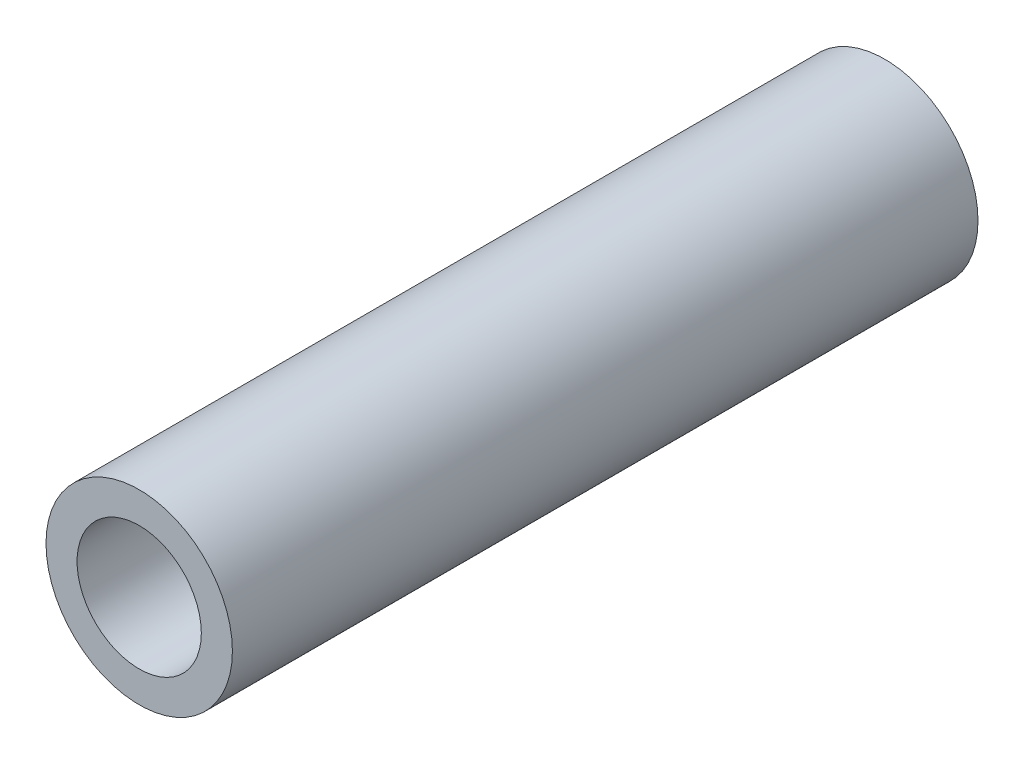
SolidWorks part; units mm, degrees
ref_plane "Front" through (0, 0, 0) normal (0, 0, 1) x (1, 0, 0)
ref_plane "Top" through (0, 0, 0) normal (0, 1, 0) x (1, 0, 0)
ref_plane "Right" through (0, 0, 0) normal (1, 0, 0) x (0, 0, -1)
sketch "Sketch1" plane through (0, 0, 0) normal (0, 0, 1) x (1, 0, 0)
  circle A0 centre (0, 0) radius 3.175
  circle A1 centre (0, 0) radius 4.7625
  dimension "D1" = 6.35
  dimension "D2" = 1.5875
extrude "Boss-Extrude1" add sketch "Sketch1" along normal blind 38.1
